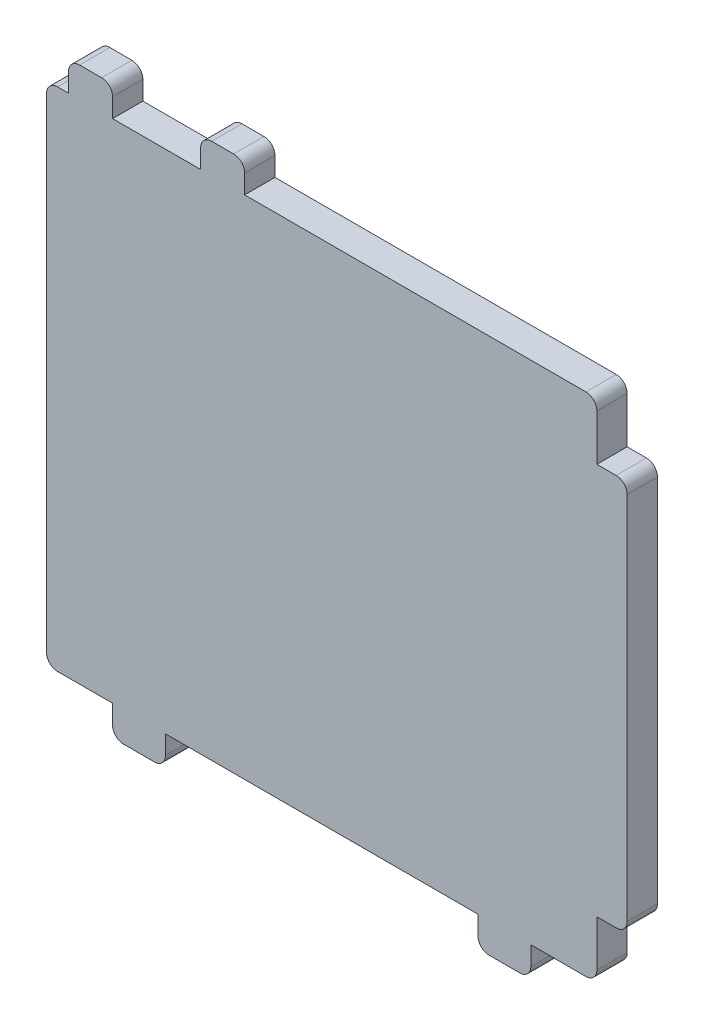
SolidWorks part; units mm, degrees
ref_plane "Front Plane" through (0, 0, 0) normal (0, 0, 1) x (1, 0, 0)
ref_plane "Top Plane" through (0, 0, 0) normal (0, 1, 0) x (1, 0, 0)
ref_plane "Right Plane" through (0, 0, 0) normal (1, 0, 0) x (0, 0, -1)
sketch "Sketch1" plane through (0, 0, 0) normal (0, 0, 1) x (1, 0, 0)
  line L1 (62.5, -57.5) -> (-62.5, -57.5)
  line L2 (62.5, -57.5) -> (62.5, 57.5)
  line L3 (62.5, 57.5) -> (-62.5, 57.5)
  line L4 (-62.5, -57.5) -> (-62.5, 57.5)
  line L5 (62.5, -57.5) -> (-62.5, 57.5) construction
  line L6 (62.5, 57.5) -> (-62.5, -57.5) construction
  point P0 (0, 0)
  dimension "D1" = 115
  dimension "D2" = 125
extrude "Boss-Extrude1" add sketch "Sketch1" along normal blind 6.88
sketch "Sketch2" plane through (0, 0, 6.88) normal (0, 0, 1) x (1, 0, 0)
  line L0 (62.5, 57.5) -> (-62.5, 57.5) construction
  line L1 (-57.5, 50.7) -> (-47.5, 50.7)
  line L2 (-57.5, 50.7) -> (-57.5, 64.3)
  line L3 (-57.5, 64.3) -> (-47.5, 64.3)
  line L4 (-47.5, 50.7) -> (-47.5, 64.3)
  line L5 (-57.5, 50.7) -> (-47.5, 64.3) construction
  line L6 (-57.5, 64.3) -> (-47.5, 50.7) construction
  line L7 (-62.5, -57.5) -> (62.5, -57.5) construction
  line L8 (-27.5, 50.7) -> (-17.5, 50.7)
  line L9 (-27.5, 50.7) -> (-27.5, 64.3)
  line L10 (-27.5, 64.3) -> (-17.5, 64.3)
  line L11 (-17.5, 50.7) -> (-17.5, 64.3)
  line L12 (-27.5, 50.7) -> (-17.5, 64.3) construction
  line L13 (-27.5, 64.3) -> (-17.5, 50.7) construction
  line L14 (-47.5, -50.7) -> (-35.5, -50.7)
  line L15 (-47.5, -50.7) -> (-47.5, -64.3)
  line L16 (-47.5, -64.3) -> (-35.5, -64.3)
  line L17 (-35.5, -50.7) -> (-35.5, -64.3)
  line L18 (-47.5, -50.7) -> (-35.5, -64.3) construction
  line L19 (-47.5, -64.3) -> (-35.5, -50.7) construction
  line L20 (-62.5, 57.5) -> (-62.5, -57.5) construction
  line L21 (47.5, -50.7) -> (35.5, -50.7)
  line L22 (47.5, -50.7) -> (47.5, -64.3)
  line L23 (47.5, -64.3) -> (35.5, -64.3)
  line L24 (35.5, -50.7) -> (35.5, -64.3)
  line L25 (47.5, -50.7) -> (35.5, -64.3) construction
  line L26 (47.5, -64.3) -> (35.5, -50.7) construction
  line L27 (62.5, -57.5) -> (62.5, 57.5) construction
  point P0 (-52.5, 57.5)
  point P7 (-22.5, 57.5)
  point P12 (-41.5, -57.5)
  point P19 (41.5, -57.5)
  dimension "D1" = 12
  dimension "D2" = 10
  dimension "D3" = 6.8
  dimension "D4" = 15
  dimension "D5" = 15
  dimension "D6" = 5
  dimension "D7" = 20
extrude "Boss-Extrude2" add sketch "Sketch2" against normal blind 6.88
sketch "Sketch3" plane through (0, 0, 6.88) normal (0, 0, 1) x (1, 0, 0)
  line L1 (55.62, -44.5) -> (69.38, -44.5)
  line L2 (55.62, -44.5) -> (55.62, 44.5)
  line L3 (55.62, 44.5) -> (69.38, 44.5)
  line L4 (69.38, -44.5) -> (69.38, 44.5)
  line L5 (55.62, -44.5) -> (69.38, 44.5) construction
  line L6 (55.62, 44.5) -> (69.38, -44.5) construction
  point P0 (62.5, 0)
  dimension "D1" = 89
  dimension "D2" = 13.76
extrude "Boss-Extrude3" add sketch "Sketch3" against normal blind 6.88
fillet "Fillet1" radius 2.5 14 edges at (-35.5, -64.3, 3.44) (-47.5, -64.3, 3.44) (62.5, -57.5, 3.44) (47.5, -64.3, 3.44) (35.5, -64.3, 3.44) (-62.5, -57.5, 3.44) (-62.5, 57.5, 3.44) (62.5, 57.5, 3.44) (-57.5, 64.3, 3.44) (-47.5, 64.3, 3.44) (-27.5, 64.3, 3.44) (-17.5, 64.3, 3.44) (69.38, -44.5, 3.44) (69.38, 44.5, 3.44)
